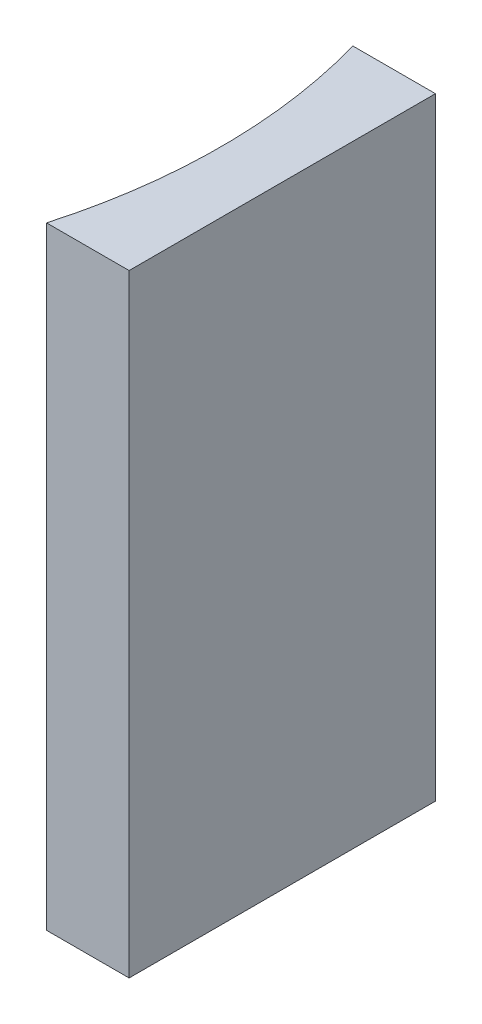
SolidWorks part; units mm, degrees
ref_plane "前视基准面" through (0, 0, 0) normal (0, 0, 1) x (1, 0, 0)
ref_plane "上视基准面" through (0, 0, 0) normal (0, 1, 0) x (1, 0, 0)
ref_plane "右视基准面" through (0, 0, 0) normal (1, 0, 0) x (0, 0, -1)
sketch "草图1" plane through (0, 0, 0) normal (0, 1, 0) x (1, 0, 0)
  line L0 (0, 0) -> (0, -10)
  line L1 (0, 0) -> (-2.6955, 0)
  line L2 (0, -10) -> (-2.6955, -10)
  line L3 (21.2259, -5) -> (-21.2259, -5) construction
  arc A0 (-2.6955, -10) -> (-2.6955, 0) centre (-20.32, -5) ccw
  point P7 (-2, -5)
  point P8 (0, -5)
  dimension "D2" = 18.32
  dimension "D3" = 2
  dimension "D1" = 10
extrude "凸台-拉伸1" add sketch "草图1" along normal blind 20
